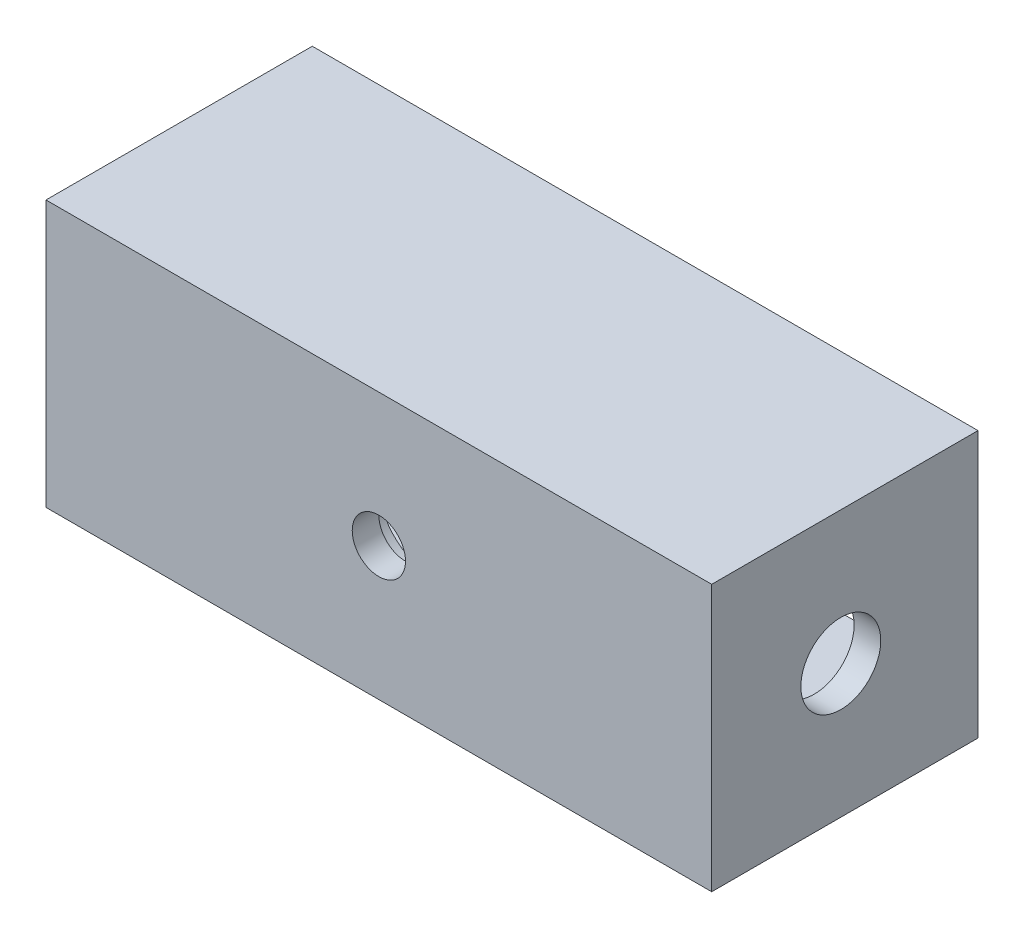
SolidWorks part; units mm, degrees
ref_plane "Front Plane" through (0, 0, 0) normal (0, 0, 1) x (1, 0, 0)
ref_plane "Top Plane" through (0, 0, 0) normal (0, 1, 0) x (1, 0, 0)
ref_plane "Right Plane" through (0, 0, 0) normal (1, 0, 0) x (0, 0, -1)
sketch "Sketch1" plane through (0, 0, 0) normal (0, 0, 1) x (1, 0, 0)
  line L1 (-12.5, 5) -> (12.5, 5)
  line L2 (-12.5, 5) -> (-12.5, -5)
  line L3 (-12.5, -5) -> (12.5, -5)
  line L4 (12.5, 5) -> (12.5, -5)
  line L5 (-12.5, 5) -> (12.5, -5) construction
  line L6 (-12.5, -5) -> (12.5, 5) construction
  point P0 (0, 0)
  dimension "D1" = 10
  dimension "D2" = 25
extrude "Boss-Extrude1" add sketch "Sketch1" along normal blind 10
sketch "Sketch2" plane through (0, 0, 0) normal (0, 0, -1) x (-1, 0, 0)
  line L1 (-11.5, 3.5) -> (11.5, 3.5)
  line L2 (-11.5, 3.5) -> (-11.5, -3.5)
  line L3 (-11.5, -3.5) -> (11.5, -3.5)
  line L4 (11.5, 3.5) -> (11.5, -3.5)
  line L5 (-11.5, 3.5) -> (11.5, -3.5) construction
  line L6 (-11.5, -3.5) -> (11.5, 3.5) construction
  point P0 (0, 0)
  dimension "D1" = 23
  dimension "D2" = 7
extrude "Cut-Extrude1" cut sketch "Sketch2" against normal blind 8
sketch "Sketch3" plane through (12.5, 0, 0) normal (1, 0, 0) x (0, 0, -1)
  circle A0 centre (-5.1522, 0) radius 1.5
  dimension "D1" = 3
extrude "Cut-Extrude2" cut sketch "Sketch3" against normal blind 51
sketch "Sketch4" plane through (0, 0, 8) normal (0, 0, -1) x (-1, 0, 0)
  circle A0 centre (0, 0) radius 2
  dimension "D1" = 4
extrude "Cut-Extrude3" cut sketch "Sketch4" against normal blind 1
sketch "Sketch5" plane through (0, 0, 9) normal (0, 0, -1) x (-1, 0, 0)
  circle A0 centre (0, 0) radius 1
  dimension "D1" = 2
extrude "Cut-Extrude4" cut sketch "Sketch5" against normal blind 4
